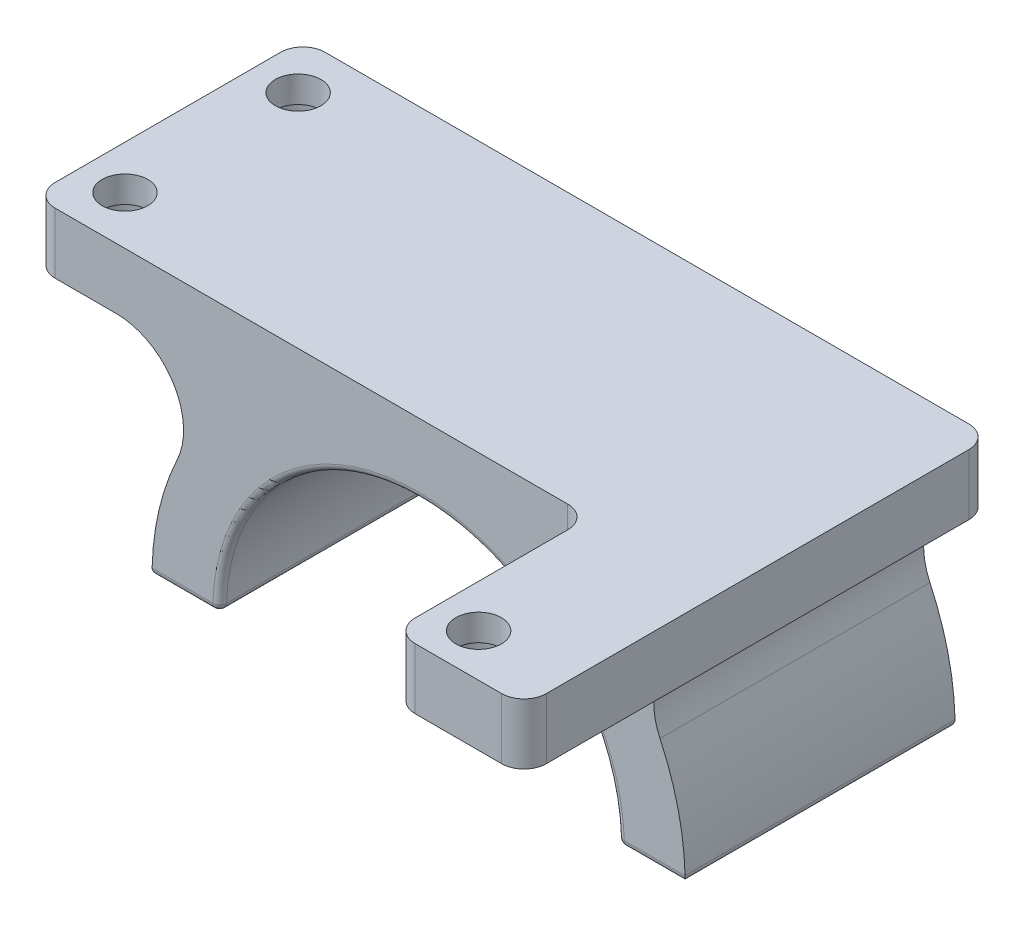
SolidWorks part; units mm, degrees
ref_plane "Front Plane" through (0, 0, 0) normal (0, 0, 1) x (1, 0, 0)
ref_plane "Top Plane" through (0, 0, 0) normal (0, 1, 0) x (1, 0, 0)
ref_plane "Right Plane" through (0, 0, 0) normal (1, 0, 0) x (0, 0, -1)
sketch "Sketch1" plane through (0, 0, 0) normal (0, 0, 1) x (1, 0, 0)
  circle A0 centre (0, 0) radius 39.5
  dimension "D1" = 79
extrude "Boss-Extrude1" add sketch "Sketch1" along normal blind 40 contours A0
sketch "Sketch2" plane through (0, 0, 0) normal (0, 0, -1) x (-1, 0, 0)
  line L0 (-39.5, 0) -> (39.5, 0)
  circle A0 centre (0, 0) radius 39.5 construction
  arc A2 (39.5, 0) -> (-39.5, 0) centre (0, 0) cw
extrude "Cut-Extrude2" cut sketch "Sketch2" against normal through all contours A2 L0
sketch "Sketch3" plane through (0, 0, 0) normal (0, 0, -1) x (-1, 0, 0)
  line L0 (-39.5, 0) -> (39.5, 0) construction
  line L1 (-29.5, 0) -> (29.5, 0)
  arc A0 (-29.5, 0) -> (29.5, 0) centre (0, 0) cw
  dimension "D1" = 29.5
extrude "Cut-Extrude3" cut sketch "Sketch3" against normal through all
fillet "Fillet2" radius 1 10 edges at (29.5, 0, 20) (-29.5, 0, 20) (0, 29.5, 40) (0, 29.5, 0) (-39.5, 0, 20) (39.5, 0, 20) (34.5, 0, 40) (-34.5, 0, 40) (34.5, 0, 0) (-34.5, 0, 0)
sketch "Sketch6" plane through (0, 0, 0) normal (0, 0, -1) x (-1, 0, 0)
  line L5 (-57.15, 40) -> (57.15, 40)
  line L6 (-57.15, 40) -> (-57.15, 31)
  line L7 (-57.15, 31) -> (57.15, 31)
  line L8 (57.15, 40) -> (57.15, 31)
  arc A0 (39.4867, 1.026) -> (-39.4867, 1.026) centre (0, 0) ccw construction
  point P9 (0, 39.5)
  point P10 (0, 31)
  dimension "D3" = 40
  dimension "D1" = 9
  dimension "D2" = 114.3
extrude "Boss-Extrude2" add sketch "Sketch6" against normal up to surface (40 mm away) up to face at (0, 12.3377, 40)
fillet "Fillet6" radius 10 2 edges at (-24.4796, 31, 20) (24.4796, 31, 20)
ref_plane "Plane1" through (-44.8247, 31, 0) normal (-1, 0, 0) x (0, 0, 1)
sketch "Sketch9" plane through (0, 40, 0) normal (0, 1, 0) x (1, 0, 0)
  line L1 (-50.6774, -7.173) -> (-50.6774, -3.7948) construction
  line L4 (-57.15, -40) -> (-57.15, 0) construction
  line L5 (-50.6774, -7.173) -> (-50.6774, -32.827) construction
  circle A0 centre (-50.6774, -7.173) radius 3.3782
  circle A1 centre (-50.6774, -32.827) radius 3.3782
  point P5 (-50.6774, -20)
  point P6 (-57.15, -20)
  dimension "D1" = 6.7564
  dimension "D2" = 6.4726
  dimension "D3" = 2
extrude "Cut-Extrude4" cut sketch "Sketch9" against normal up to surface (10.8916 mm away)
sketch "Sketch10" plane through (0, 40, 0) normal (0, 1, 0) x (1, 0, 0)
  line L0 (57.15, -40) -> (57.15, 0) construction
  circle A0 centre (50.8, -23.937) radius 3.3782
  circle A1 centre (50.8, -61.529) radius 3.3782
  circle A3 centre (-50.6774, -7.173) radius 3.3782 construction
  dimension "D1" = 6.7564
  dimension "D3" = 16.764
  dimension "D4" = 6.35
  dimension "D2" = 2
sketch "Sketch11" plane through (0, 0, 40) normal (0, 0, 1) x (1, 0, 0)
  line L0 (-57.15, 40) -> (57.15, 40) construction
  line L1 (25.4, 40) -> (57.15, 40)
  line L2 (25.4, 40) -> (25.4, 31)
  line L3 (25.4, 31) -> (57.15, 31)
  line L4 (57.15, 40) -> (57.15, 31)
  dimension "D1" = 31.75
extrude "Boss-Extrude3" add sketch "Sketch11" along normal blind 29.21
sketch "Sketch12" plane through (0, 40, 0) normal (0, 1, 0) x (1, 0, 0)
  circle A0 centre (50.8, -23.937) radius 3.3782 construction
  circle A1 centre (50.8, -23.937) radius 3.3782
  circle A2 centre (50.8, -61.529) radius 3.3782 construction
  circle A3 centre (50.8, -61.529) radius 3.3782
sketch "Sketch4" plane through (0, 0, 0) normal (0, -1, 0) x (1, 0, 0)
  line L0 (38.487, 40) -> (30.5, 40) construction
  line L1 (32.9841, 35) -> (35.987, 35)
  line L2 (32.9841, 35) -> (32.9841, 5)
  line L3 (32.9841, 5) -> (35.987, 5)
  line L4 (35.987, 35) -> (35.987, 5)
  line L5 (38.487, 0) -> (-30.5, 0) construction
  line L7 (39.487, 0) -> (39.487, 40) construction
  line L8 (29.4841, 1) -> (29.4841, 39) construction
  line L9 (0, 0) -> (0, 64.0682) construction
  dimension "D1" = 5
  dimension "D2" = 5
  dimension "D3" = 3.5
  dimension "D4" = 3.5
revolve "Cut-Revolve1" cut sketch "Sketch4" angle 360 about L9
fillet "Fillet7" radius 3.302 6 edges at (-57.15, 35.5, 40) (-57.15, 35.5, 0) (57.15, 35.5, 69.21) (57.15, 35.5, 0) (25.4, 35.5, 69.21) (25.4, 35.5, 40)
sketch "Sketch13" plane through (0, 31, 0) normal (0, -1, 0) x (1, 0, 0)
  circle A0 centre (-50.6774, 32.827) radius 5.08
  circle A1 centre (-50.6774, 32.827) radius 3.3782 construction
  circle A2 centre (-50.6774, 7.173) radius 5.08
  dimension "D1" = 10.16
  dimension "D2" = 2
extrude "Cut-Extrude6" cut sketch "Sketch13" against normal blind 5.08
sketch "Sketch14" plane through (0, 31, 0) normal (0, -1, 0) x (1, 0, 0)
  circle A0 centre (50.8, 61.529) radius 5.08
  circle A1 centre (50.8, 24.191) radius 5.08
  dimension "D1" = 10.16
  dimension "D2" = 2
sketch "Sketch15" plane through (0, 31, 0) normal (0, -1, 0) x (1, 0, 0)
  line L0 (25.4, 65.908) -> (25.4, 43.302) construction
  line L2 (28.702, 69.21) -> (53.848, 69.21) construction
  circle A0 centre (31.75, 62.86) radius 3.3782
  dimension "D1" = 6.7564
  dimension "D2" = 6.35
  dimension "D3" = 6.35
extrude "Cut-Extrude8" cut sketch "Sketch15" against normal through all
sketch "Sketch16" plane through (0, 31, 0) normal (0, -1, 0) x (1, 0, 0)
  circle A0 centre (31.75, 62.86) radius 5.08
  circle A1 centre (31.75, 62.86) radius 3.3782 construction
  dimension "D1" = 10.16
extrude "Cut-Extrude9" cut sketch "Sketch16" against normal blind 5.08
sketch "Sketch17" plane through (0, 31, 0) normal (0, -1, 0) x (1, 0, 0)
  line L1 (44.8247, 0) -> (81.4109, 0)
  line L2 (44.8247, 0) -> (44.8247, 70.8356)
  line L3 (44.8247, 70.8356) -> (81.4109, 70.8356)
  line L4 (81.4109, 0) -> (81.4109, 70.8356)
extrude "Cut-Extrude10" cut sketch "Sketch17" against normal through all
fillet "Fillet8" radius 3.302 2 edges at (44.8247, 35.5, 69.21) (44.8247, 35.5, 0)
mirror "Mirror7" [suppressed]
mirror "Mirror8" about plane through (-57.15, 40, 154.6538) normal (-1, 0, 0) of bodies 116
delete or keep bodies "Body-Delete/Keep 2" type delete bodies bodies 119
